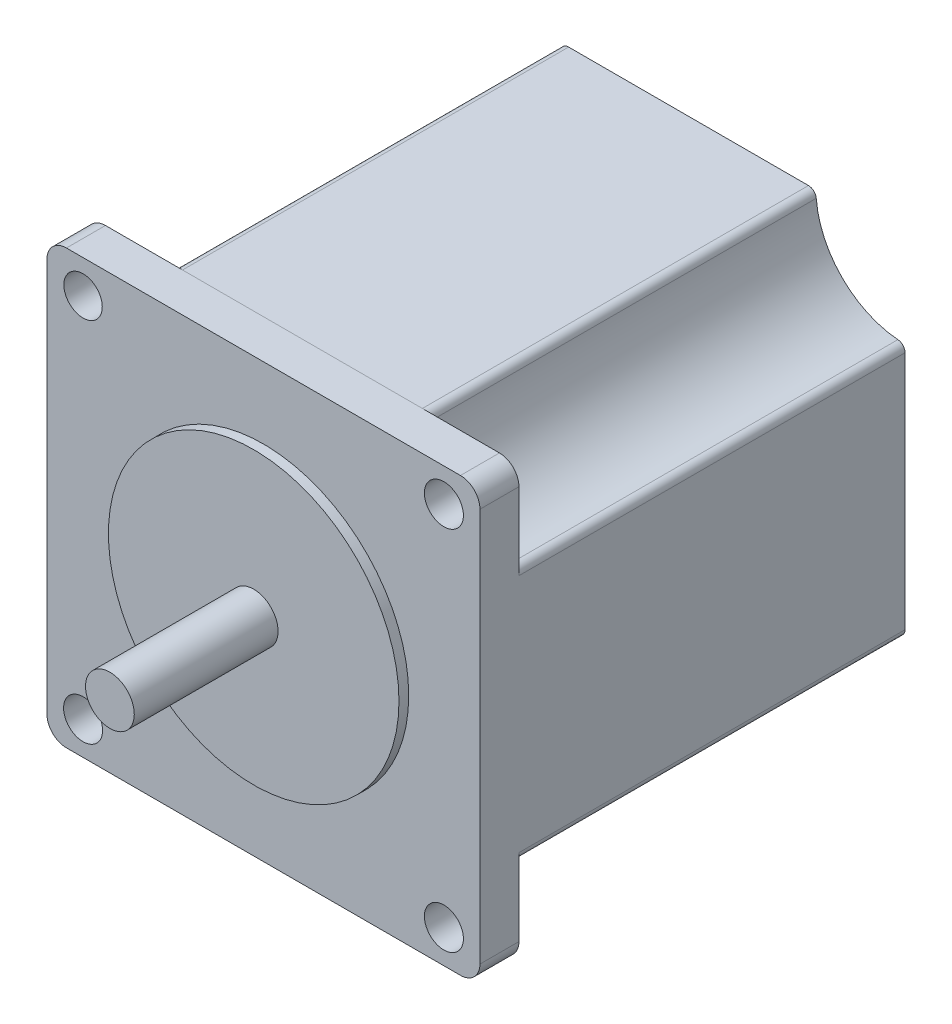
SolidWorks part; units mm, degrees
ref_plane "Front Plane" through (0, 0, 0) normal (0, 0, 1) x (1, 0, 0)
ref_plane "Top Plane" through (0, 0, 0) normal (0, 1, 0) x (1, 0, 0)
ref_plane "Right Plane" through (0, 0, 0) normal (1, 0, 0) x (0, 0, -1)
sketch "Sketch1" plane through (0, 0, 0) normal (0, 0, 1) x (1, 0, 0)
  line L1 (-25.66, 28.194) -> (25.66, 28.194)
  line L2 (-28.2, 25.654) -> (-28.2, -25.654)
  line L3 (-25.66, -28.194) -> (25.66, -28.194)
  line L4 (28.2, 25.654) -> (28.2, -25.654)
  line L5 (-28.2, 28.194) -> (28.2, -28.194) construction
  line L6 (-28.2, -28.194) -> (28.2, 28.194) construction
  arc A0 (-28.2, -25.654) -> (-25.66, -28.194) centre (-25.66, -25.654) ccw
  arc A1 (25.66, -28.194) -> (28.2, -25.654) centre (25.66, -25.654) ccw
  arc A2 (25.66, 28.194) -> (28.2, 25.654) centre (25.66, 25.654) cw
  arc A3 (-25.66, 28.194) -> (-28.2, 25.654) centre (-25.66, 25.654) ccw
  point P0 (0, 0)
  dimension "D3" = 2.54
  dimension "D1" = 56.4
  dimension "D2" = 56.388
extrude "Boss-Extrude1" add sketch "Sketch1" against normal blind 5.08
sketch "Sketch2" plane through (0, 0, 0) normal (0, 0, 1) x (1, 0, 0)
  circle A0 centre (-23.495, 23.876) radius 2.5
  circle A1 centre (23.505, 23.876) radius 2.54
  circle A2 centre (-23.495, -23.876) radius 2.54
  circle A3 centre (23.505, -23.876) radius 2.54
  dimension "D1" = 5
  dimension "D2" = 5.08
  dimension "D3" = 47
  dimension "D4" = 23.495
  dimension "D5" = 5.08
  dimension "D6" = 5.08
  dimension "D8" = 23.495
  dimension "D7" = 47
  dimension "D9" = 23.876
  dimension "D10" = 23.876
extrude "Cut-Extrude1" cut sketch "Sketch2" against normal blind 12.7
sketch "Sketch3" plane through (0, 0, 0) normal (0, 0, 1) x (1, 0, 0)
  circle A0 centre (0, 0) radius 3.175
  dimension "D1" = 6.35
extrude "Boss-Extrude2" add sketch "Sketch3" along normal blind 20
sketch "Sketch6" plane through (0, 0, -5.08) normal (0, 0, -1) x (-1, 0, 0)
  line L0 (-15.6206, 28.194) -> (15.6206, 28.194)
  line L1 (-25.66, 28.194) -> (25.66, 28.194) construction
  line L2 (-28.2, 15.6189) -> (-28.2, -15.6189)
  line L3 (-28.2, -25.654) -> (-28.2, 25.654) construction
  line L4 (-15.6202, -28.194) -> (15.6202, -28.194)
  line L5 (25.66, -28.194) -> (-25.66, -28.194) construction
  line L6 (28.2, 15.6184) -> (28.2, -15.6184)
  line L7 (28.2, 25.654) -> (28.2, -25.654) construction
  arc A0 (16.6329, -27.26) -> (27.2656, -16.6311) centre (28.1977, -28.1963) cw
  arc A1 (-27.2656, -16.6317) -> (-16.6329, -27.26) centre (-28.1974, -28.1966) cw
  arc A2 (-16.6333, 27.26) -> (-27.2656, 16.6317) centre (-28.1976, 28.1964) cw
  arc A3 (27.2657, 16.6311) -> (16.6333, 27.26) centre (28.1979, 28.1961) cw
  arc A4 (-15.6202, -28.194) -> (-16.6329, -27.26) centre (-15.6202, -27.178) cw
  arc A5 (15.6202, -28.194) -> (16.6329, -27.26) centre (15.6202, -27.178) ccw
  arc A6 (28.2, -15.6184) -> (27.2656, -16.6311) centre (27.184, -15.6184) cw
  arc A7 (28.2, 15.6184) -> (27.2657, 16.6311) centre (27.184, 15.6184) ccw
  arc A8 (-28.2, -15.6189) -> (-27.2656, -16.6317) centre (-27.184, -15.6189) ccw
  arc A9 (-28.2, 15.6189) -> (-27.2656, 16.6317) centre (-27.184, 15.6189) cw
  arc A10 (-15.6206, 28.194) -> (-16.6333, 27.26) centre (-15.6206, 27.178) ccw
  arc A11 (15.6206, 28.194) -> (16.6333, 27.26) centre (15.6206, 27.178) cw
  point P16 (-28.2, 0)
  point P17 (0, 28.194)
  point P18 (28.2, 0)
  point P19 (0, -28.194)
  point P27 (18.8596, 28.194)
  point P30 (28.2, 18.8589)
  point P33 (28.2, -18.8601)
  point P36 (18.8601, -28.194)
  point P39 (-18.8589, -28.194)
  point P42 (-28.2, -18.8595)
  point P45 (-28.2, 18.8595)
  point P48 (-18.8594, 28.194)
  dimension "D5" = 1.016
  dimension "D1" = 37.719
  dimension "D2" = 37.719
  dimension "D3" = 37.719
  dimension "D4" = 37.719
extrude "Boss-Extrude3" add sketch "Sketch6" along normal blind 50.292
sketch "Sketch7" plane through (0, 0, -55.372) normal (0, 0, -1) x (-1, 0, 0)
  circle A0 centre (0, 0) radius 5.08
  dimension "D1" = 10.16
extrude "Cut-Extrude2" cut sketch "Sketch7" against normal blind 2.54
sketch "Sketch8" plane through (0, -28.194, 0) normal (0, -1, 0) x (-1, 0, 0)
  line L0 (-15.6202, 55.372) -> (15.6202, 55.372) construction
  line L1 (-2.2225, 51.562) -> (2.2225, 51.562)
  line L2 (-2.2225, 51.562) -> (-2.2225, 47.117)
  line L3 (-2.2225, 47.117) -> (2.2225, 47.117)
  line L4 (2.2225, 51.562) -> (2.2225, 47.117)
  line L5 (-2.2225, 51.562) -> (2.2225, 47.117) construction
  line L6 (-2.2225, 47.117) -> (2.2225, 51.562) construction
  point P0 (0, 49.3395)
  dimension "D1" = 4.445
  dimension "D2" = 4.445
  dimension "D3" = 2.2225
  dimension "D4" = 3.81
extrude "Boss-Extrude4" add sketch "Sketch8" along normal blind 2.54
sketch "Sketch9" plane through (0, 0, 0) normal (0, 0, 1) x (1, 0, 0)
  circle A0 centre (0, 0) radius 18.923
  dimension "D1" = 37.846
extrude "Boss-Extrude5" add sketch "Sketch9" along normal blind 1.27
